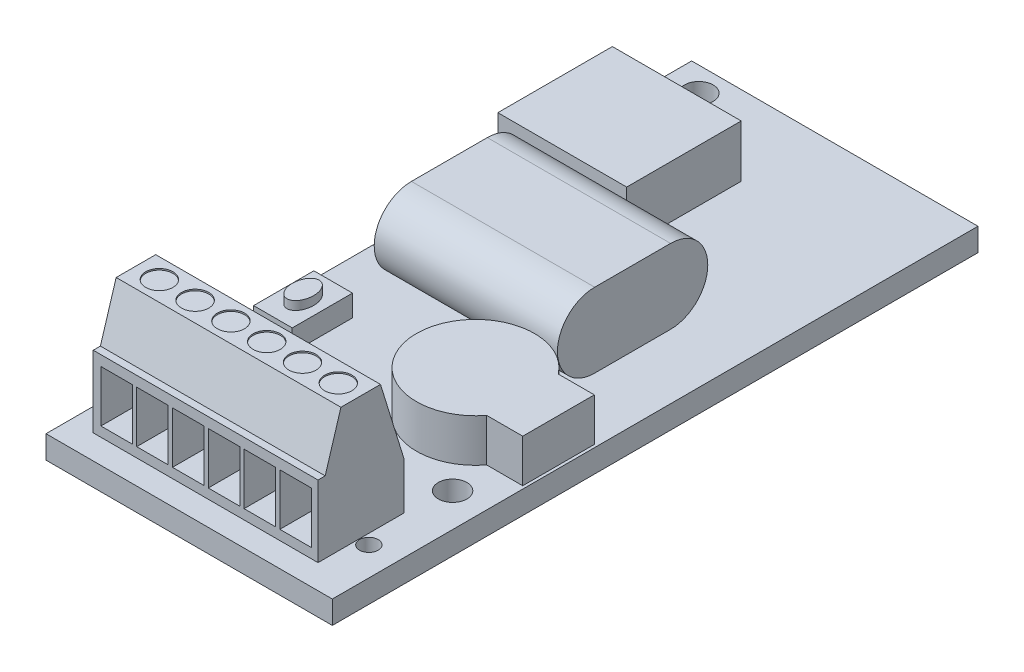
SolidWorks part; units mm, degrees
ref_plane "Front Plane" through (0, 0, 0) normal (0, 0, 1) x (1, 0, 0)
ref_plane "Top Plane" through (0, 0, 0) normal (0, 1, 0) x (1, 0, 0)
ref_plane "Right Plane" through (0, 0, 0) normal (1, 0, 0) x (0, 0, -1)
sketch "Sketch1" plane through (0, 0, 0) normal (0, 1, 0) x (1, 0, 0)
  line L1 (0, 0) -> (20, 0)
  line L2 (0, 0) -> (0, 45.1)
  line L3 (0, 45.1) -> (20, 45.1)
  line L4 (20, 0) -> (20, 45.1)
  circle A0 centre (2.2, 43.4) radius 1
  circle A1 centre (17.65, 10.75) radius 1
  circle A2 centre (18, 4.55) radius 0.65
  point P13 (17.0293, 0)
  dimension "D3" = 1.3
  dimension "D4" = 2
  dimension "D5" = 2
  dimension "D1" = 20
  dimension "D2" = 45.1
  dimension "D6" = 1.7
  dimension "D7" = 2.2
  dimension "D8" = 2.35
  dimension "D9" = 10.75
  dimension "D10" = 4.55
  dimension "D11" = 2
extrude "Boss-Extrude1" add sketch "Sketch1" along normal blind 1.6
sketch "Sketch2" plane through (0, 1.6, 0) normal (0, 1, 0) x (1, 0, 0)
  line L1 (17.3, 7.7) -> (1.6, 7.7)
  line L2 (17.3, 7.7) -> (17.3, 1.7)
  line L3 (17.3, 1.7) -> (1.6, 1.7)
  line L4 (1.6, 7.7) -> (1.6, 1.7)
  line L5 (0, 0) -> (20, 0) construction
  line L6 (0, 45.1) -> (0, 0) construction
  dimension "D1" = 6
  dimension "D2" = 15.7
  dimension "D3" = 1.6
  dimension "D4" = 1.7
extrude "Boss-Extrude2" add sketch "Sketch2" along normal blind 8.6
sketch "Sketch3" plane through (17.3, 0, 0) normal (1, 0, 0) x (0, 0, -1)
  line L0 (1.7, 6.6) -> (2.2, 6.6)
  line L1 (1.7, 10.2) -> (1.7, 1.6) construction
  line L2 (1.7, 1.6) -> (7.7, 1.6) construction
  line L3 (2.2, 6.6) -> (3.3, 10.2)
  line L4 (1.7, 10.2) -> (7.7, 10.2) construction
  line L5 (3.3, 10.2) -> (1.7, 10.2)
  line L6 (1.7, 10.2) -> (1.7, 6.6)
  line L7 (6.0637, 10.2) -> (7.7, 10.2)
  line L8 (7.7, 10.2) -> (7.7, 1.6) construction
  line L9 (6.0637, 10.2) -> (7.7, 4.9017)
  line L10 (7.7, 10.2) -> (7.7, 4.9017)
  dimension "D1" = 5
  dimension "D2" = 0.5
  dimension "D3" = 1.6
extrude "Cut-Extrude1" cut sketch "Sketch3" against normal through all
sketch "Sketch4" plane through (0, 0, -1.7) normal (0, 0, 1) x (1, 0, 0)
  line L0 (4.6358, 5.8845) -> (6.8358, 5.8845)
  line L1 (2.1358, 5.8845) -> (4.3358, 5.8845)
  line L2 (2.1358, 5.8845) -> (2.1358, 2.2831)
  line L3 (2.1358, 2.2831) -> (4.3358, 2.2831)
  line L4 (4.3358, 5.8845) -> (4.3358, 2.2831)
  line L5 (6.8358, 5.8845) -> (6.8358, 2.2831)
  line L6 (4.6358, 2.2831) -> (6.8358, 2.2831)
  line L7 (4.6358, 5.8845) -> (4.6358, 2.2831)
  line L8 (7.1358, 5.8845) -> (9.3358, 5.8845)
  line L9 (9.3358, 5.8845) -> (9.3358, 2.2831)
  line L10 (7.1358, 2.2831) -> (9.3358, 2.2831)
  line L11 (7.1358, 5.8845) -> (7.1358, 2.2831)
  line L12 (9.6358, 5.8845) -> (11.8358, 5.8845)
  line L13 (11.8358, 5.8845) -> (11.8358, 2.2831)
  line L14 (9.6358, 2.2831) -> (11.8358, 2.2831)
  line L15 (9.6358, 5.8845) -> (9.6358, 2.2831)
  line L16 (12.1358, 5.8845) -> (14.3358, 5.8845)
  line L17 (14.3358, 5.8845) -> (14.3358, 2.2831)
  line L18 (12.1358, 2.2831) -> (14.3358, 2.2831)
  line L19 (12.1358, 5.8845) -> (12.1358, 2.2831)
  line L20 (14.6358, 5.8845) -> (16.8358, 5.8845)
  line L21 (16.8358, 5.8845) -> (16.8358, 2.2831)
  line L22 (14.6358, 2.2831) -> (16.8358, 2.2831)
  line L23 (14.6358, 5.8845) -> (14.6358, 2.2831)
  dimension "D1" = 2.2
  dimension "D2" = 6
extrude "Cut-Extrude2" cut sketch "Sketch4" against normal blind 4
sketch "Sketch5" plane through (0, 10.2, 0) normal (0, 1, 0) x (1, 0, 0)
  line L0 (1.6, 6.0637) -> (1.6, 3.3) construction
  line L2 (4.3358, 1.7) -> (2.1358, 1.7) construction
  circle A0 centre (3.2358, 4.6819) radius 0.95
  circle A1 centre (5.7358, 4.6819) radius 0.95
  circle A2 centre (8.2358, 4.6819) radius 0.95
  circle A3 centre (10.7358, 4.6819) radius 0.95
  circle A4 centre (13.2358, 4.6819) radius 0.95
  circle A5 centre (15.7358, 4.6819) radius 0.95
  point P4 (1.6, 4.6819)
  point P7 (3.2358, 1.7)
  dimension "D2" = 1.9
  dimension "D1" = 0
  dimension "D3" = 0
  dimension "D4" = 6
extrude "Cut-Extrude3" cut sketch "Sketch5" against normal blind 0.1
sketch "Sketch6" plane through (0, 1.6, 0) normal (0, 1, 0) x (1, 0, 0)
  line L0 (0, 0) -> (20, 0) construction
  line L1 (1, 17.71) -> (3.7, 17.71)
  line L2 (1, 17.71) -> (1, 13.5)
  line L3 (1, 13.5) -> (3.7, 13.5)
  line L4 (3.7, 17.71) -> (3.7, 13.5)
  line L5 (0, 45.1) -> (0, 0) construction
  dimension "D1" = 4.21
  dimension "D2" = 2.7
  dimension "D3" = 13.5
  dimension "D4" = 1
extrude "Boss-Extrude3" add sketch "Sketch6" along normal blind 1.5
sketch "Sketch7" plane through (0, 3.1, 0) normal (0, 1, 0) x (1, 0, 0)
  ellipse E0 centre (2.35, 15.605) end of major axis (2.35, 16.7293) minor radius 0.7438
extrude "Boss-Extrude4" add sketch "Sketch7" along normal blind 0.6
sketch "Sketch8" plane through (0, 1.6, 0) normal (0, 1, 0) x (1, 0, 0)
  line L0 (20, 0) -> (20, 45.1) construction
  line L2 (0, 0) -> (20, 0) construction
  line L4 (17.2811, 13.5) -> (19.8, 13.5)
  line L6 (17.2811, 18.5) -> (19.8, 18.5)
  line L7 (19.8, 13.5) -> (19.8, 18.5)
  arc A0 (17.2811, 18.5) -> (17.2811, 13.5) centre (14, 16) ccw
  point P4 (17.5572, 16)
  dimension "D1" = 8.25
  dimension "D2" = 6
  dimension "D3" = 16
  dimension "D4" = 5
  dimension "D5" = 0
  dimension "D6" = 0.2
extrude "Boss-Extrude5" add sketch "Sketch8" along normal blind 3
ref_plane "Plane1" through (15.5, 0, 0) normal (1, 0, 0) x (0, 0, -1)
sketch "Sketch9" plane through (15.5, 0, 0) normal (1, 0, 0) x (0, 0, -1)
  line L0 (22.825, 4.2) -> (28.125, 4.2) construction
  line L1 (22.825, 6.8) -> (28.125, 6.8)
  line L2 (22.825, 1.6) -> (28.125, 1.6)
  line L3 (0, 1.6) -> (45.1, 1.6) construction
  arc A0 (22.825, 6.8) -> (22.825, 1.6) centre (22.825, 4.2) ccw
  arc A1 (28.125, 1.6) -> (28.125, 6.8) centre (28.125, 4.2) ccw
  point P2 (25.475, 4.2)
  point P10 (20.225, 4.2)
  dimension "D1" = 5.2
  dimension "D2" = 5.3
  dimension "D3" = 0
  dimension "D4" = 0.1
extrude "Boss-Extrude6" add sketch "Sketch9" against normal blind 12.8
sketch "Sketch10" plane through (0, 1.6, 0) normal (0, 1, 0) x (1, 0, 0)
  line L0 (0, 45.1) -> (0, 0) construction
  line L1 (0.01, 31.55) -> (9.01, 31.55)
  line L2 (0.01, 31.55) -> (0.01, 39.55)
  line L3 (0.01, 39.55) -> (9.01, 39.55)
  line L4 (9.01, 31.55) -> (9.01, 39.55)
  line L5 (20, 45.1) -> (0, 45.1) construction
  dimension "D1" = 0.01
  dimension "D2" = 8
  dimension "D3" = 9
  dimension "D4" = 5.55
extrude "Boss-Extrude7" add sketch "Sketch10" along normal blind 3.65
